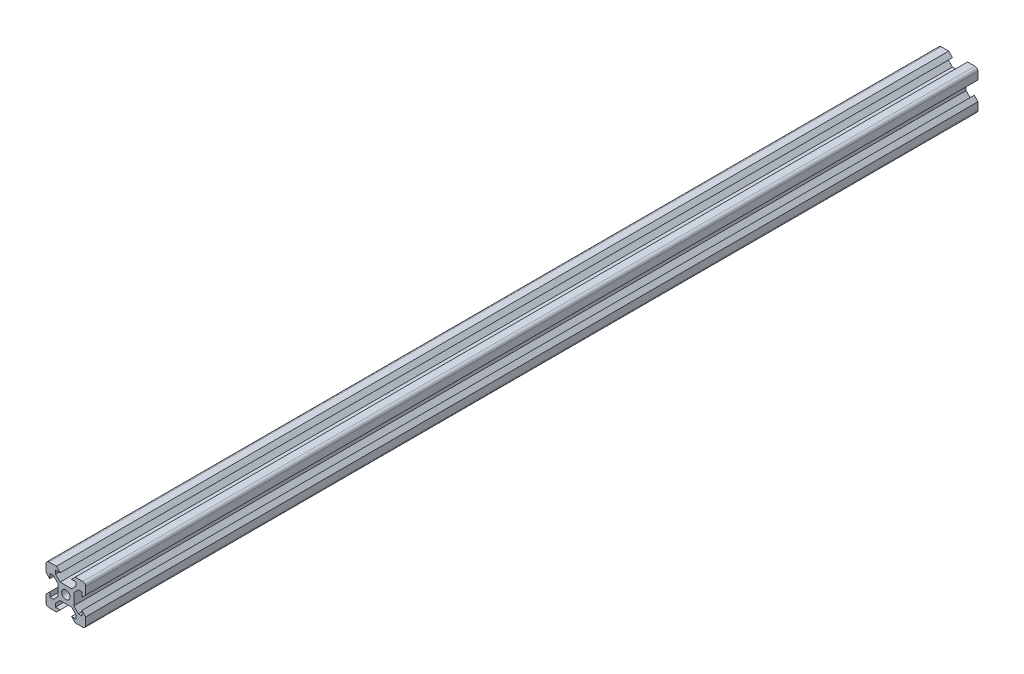
SolidWorks part; units mm, degrees
ref_plane "Front Plane" through (0, 0, 0) normal (0, 0, 1) x (1, 0, 0)
ref_plane "Top Plane" through (0, 0, 0) normal (0, 1, 0) x (1, 0, 0)
ref_plane "Right Plane" through (0, 0, 0) normal (1, 0, 0) x (0, 0, -1)
sketch "Sketch1" plane through (0, 0, 0) normal (0, 0, 1) x (1, 0, 0)
  line L0 (15.6876, 55.3211) -> (115.0437, 55.3211) construction
  line L1 (8.1, 5.225) -> (8.1, 2.85)
  line L2 (-8.5, 10) -> (-4.75, 10)
  line L3 (-10, 8.5) -> (-10, 4.75)
  line L4 (-8.5, -10) -> (-4.75, -10)
  line L5 (10, 8.5) -> (10, 4.75)
  line L6 (6.325, 5.225) -> (4, 2.9)
  line L7 (-8.1, -2.85) -> (-8.1, -5.225)
  line L8 (-2.9, 4) -> (2.9, 4)
  line L9 (-4, 2.9) -> (-4, -2.9)
  line L10 (-2.9, -4) -> (2.9, -4)
  line L11 (4, 2.9) -> (4, -2.9)
  line L12 (2.85, -8.1) -> (5.225, -8.1)
  line L13 (-5.225, -8.1) -> (-2.85, -8.1)
  line L14 (5.225, 6.325) -> (2.9, 4)
  line L17 (-10, 4.75) -> (-8.1, 2.85)
  line L20 (4.75, -10) -> (8.5, -10)
  line L22 (-10, -4.75) -> (-10, -8.5)
  line L23 (10, -4.75) -> (10, -8.5)
  line L24 (-10, -4.75) -> (-8.1, -2.85)
  line L25 (-4.75, -10) -> (-2.85, -8.1)
  line L26 (4.75, -10) -> (2.85, -8.1)
  line L27 (10, -4.75) -> (8.1, -2.85)
  line L28 (10, 4.75) -> (8.1, 2.85)
  line L29 (-4.75, 10) -> (-2.85, 8.1)
  line L30 (4.75, 10) -> (2.85, 8.1)
  line L31 (8.1, -2.85) -> (8.1, -5.225)
  line L32 (6.325, -5.225) -> (8.1, -5.225)
  line L33 (5.225, -6.325) -> (5.225, -8.1)
  line L34 (4.75, 10) -> (8.5, 10)
  line L35 (2.85, 8.1) -> (5.225, 8.1)
  line L36 (10, -10) -> (10.975, -10.975) construction
  line L37 (-5.225, 8.1) -> (-2.85, 8.1)
  line L38 (-8.1, -5.225) -> (-6.325, -5.225)
  line L39 (-5.225, 6.325) -> (-2.9, 4)
  line L40 (-8.1, 5.225) -> (-8.1, 2.85)
  line L41 (-5.225, -6.325) -> (-5.225, -8.1)
  line L42 (-6.325, 5.225) -> (-4, 2.9)
  line L46 (-8.1, 5.225) -> (-6.325, 5.225)
  line L47 (-5.225, 8.1) -> (-5.225, 6.325)
  line L52 (8.1, 5.225) -> (6.325, 5.225)
  line L53 (5.225, 8.1) -> (5.225, 6.325)
  line L63 (4, -2.9) -> (6.325, -5.225)
  line L66 (2.9, -4) -> (5.225, -6.325)
  line L67 (-2.9, -4) -> (-5.225, -6.325)
  line L70 (-4, -2.9) -> (-6.325, -5.225)
  arc A0 (-8.5, -10) -> (-10, -8.5) centre (-8.5, -8.5) cw
  arc A1 (8.5, -10) -> (10, -8.5) centre (8.5, -8.5) ccw
  arc A2 (10, 8.5) -> (8.5, 10) centre (8.5, 8.5) ccw
  arc A3 (-8.5, 10) -> (-10, 8.5) centre (-8.5, 8.5) ccw
  circle A4 centre (0, 0) radius 2.125
  point P2 (0, 0)
  point P8 (0, 0)
  point P14 (-10, -10)
  point P20 (0, 0)
  point P49 (10, 10)
  point P52 (-10, 10)
  dimension "D3" = 1.5
  dimension "D4" = 4.25
  dimension "D1" = 20
  dimension "D2" = 20
  dimension "D13" = 5.25
  dimension "D14" = 5.25
  dimension "D15" = 90
  dimension "D16" = 5.25
  dimension "D17" = 5.25
  dimension "D18" = 5.25
  dimension "D19" = 5.25
  dimension "D20" = 5.25
  dimension "D21" = 5.25
  dimension "D22" = 90
  dimension "D23" = 90
  dimension "D24" = 90
  dimension "D25" = 2.85
  dimension "D26" = 2.85
  dimension "D27" = 2.85
  dimension "D28" = 2.85
extrude "Boss-Extrude1" add sketch "Sketch1" along normal blind 450
